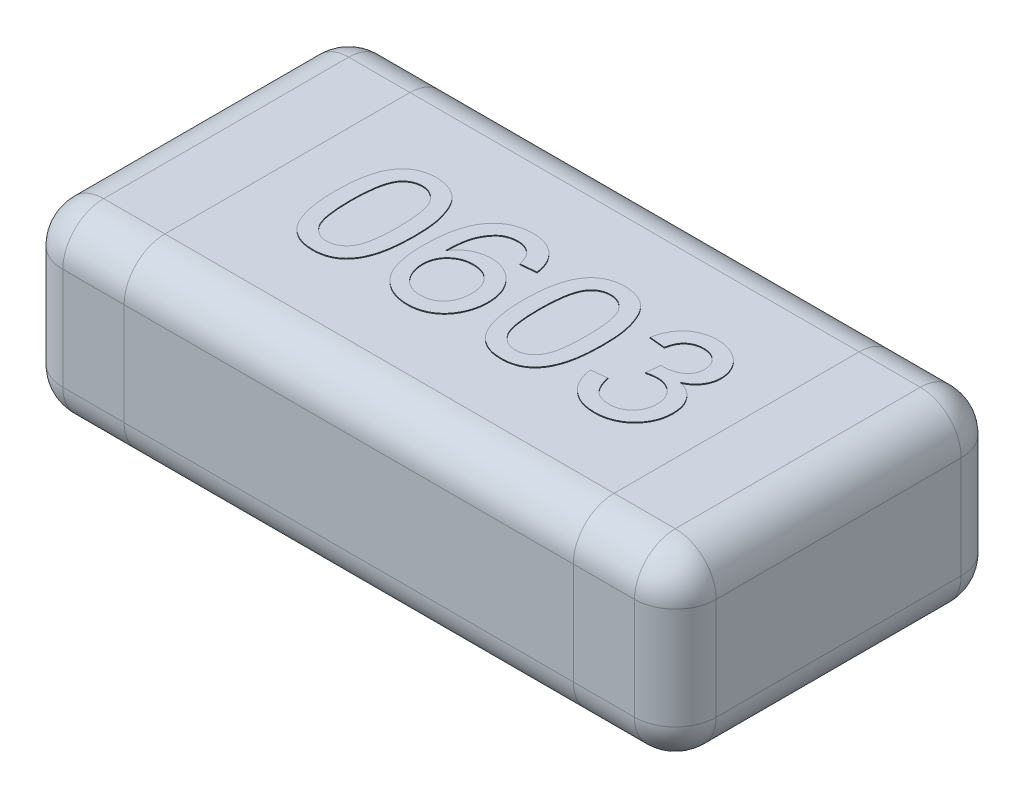
SolidWorks part; units mm, degrees
ref_plane "Front" through (0, 0, 0) normal (0, 0, 1) x (1, 0, 0)
ref_plane "Top" through (0, 0, 0) normal (0, 1, 0) x (1, 0, 0)
ref_plane "Right" through (0, 0, 0) normal (1, 0, 0) x (0, 0, -1)
sketch "Sketch1" plane through (0, 0, 0) normal (0, 1, 0) x (1, 0, 0)
  line L0 (0, -5.3126) -> (0, 5.729) construction
  line L1 (-6.1479, 0) -> (7.7291, 0) construction
  line L3 (-0.8, 0.4) -> (0.8, 0.4)
  line L4 (-0.8, 0.4) -> (-0.8, -0.4)
  line L5 (-0.8, -0.4) -> (0.8, -0.4)
  line L6 (0.8, 0.4) -> (0.8, -0.4)
  dimension "D1" = 1.6
  dimension "D2" = 0.8
extrude "Extrude1" add sketch "Sketch1" along normal blind 0.45
fillet "Fillet1" radius 0.1 12 edges at (0, 0.45, 0.4) (-0.8, 0.225, -0.4) (0, 0, -0.4) (-0.8, 0, 0) (-0.8, 0.225, 0.4) (0, 0, 0.4) (0.8, 0.225, 0.4) (0.8, 0.225, -0.4) (0.8, 0, 0) (0, 0.45, -0.4) (0.8, 0.45, 0) (-0.8, 0.45, 0)
sketch "Sketch2" plane through (0, 0, 0.4) normal (0, 0, 1) x (1, 0, 0)
  line L0 (-0.7, 0.45) -> (0.7, 0.45) construction
  line L1 (-0.55, 0.45) -> (0.55, 0.45)
  line L2 (-0.55, 0.45) -> (-0.55, 0)
  line L3 (-0.55, 0) -> (0.55, 0)
  line L4 (0.55, 0.45) -> (0.55, 0)
  line L5 (0.7, 0) -> (-0.7, 0) construction
  line L6 (-0.8, 0.1) -> (-0.8, 0.35) construction
  line L7 (0, -0.2963) -> (0, 3.0124) construction
  dimension "D1" = 0.25
split line "Split Line1"
sketch "Sketch3" plane through (0, 0.45, 0) normal (0, 1, 0) x (1, 0, 0)
  text T0 "0603" font "Arial" height 0.3
  dimension "D1" = 0.45
  dimension "D2" = 0.15
extrude "Extrude2" add sketch "Sketch3" along normal blind 0.002
